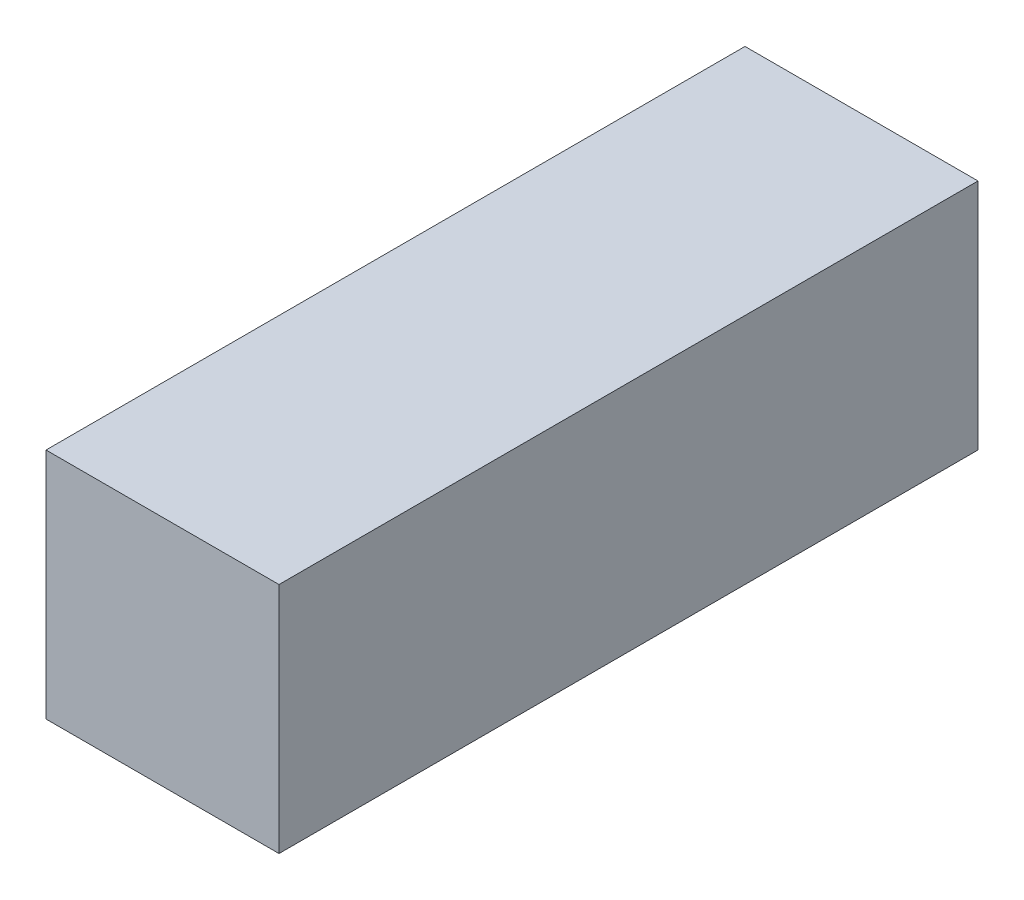
SolidWorks part; units mm, degrees
ref_plane "Front Plane" through (0, 0, 0) normal (0, 0, 1) x (1, 0, 0)
ref_plane "Top Plane" through (0, 0, 0) normal (0, 1, 0) x (1, 0, 0)
ref_plane "Right Plane" through (0, 0, 0) normal (1, 0, 0) x (0, 0, -1)
sketch "Sketch1" plane through (0, 0, 0) normal (0, 1, 0) x (1, 0, 0)
  line L1 (-57.5042, 259.0381) -> (142.4958, 259.0381)
  line L2 (-57.5042, 259.0381) -> (-57.5042, -340.9619)
  line L3 (-57.5042, -340.9619) -> (142.4958, -340.9619)
  line L4 (142.4958, 259.0381) -> (142.4958, -340.9619)
  dimension "D1" = 200
  dimension "D2" = 600
extrude "Boss-Extrude1" add sketch "Sketch1" along normal blind 200
